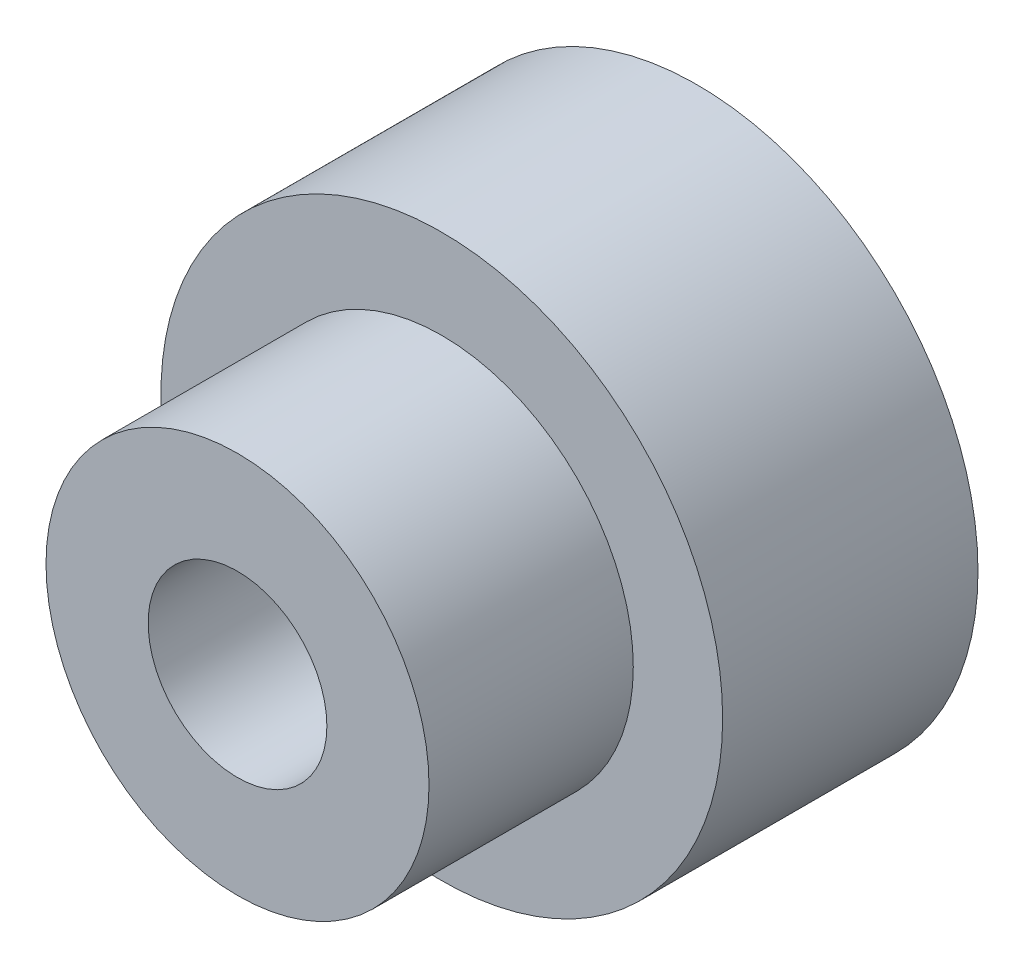
SolidWorks part; units mm, degrees
ref_plane "前视基准面" through (0, 0, 0) normal (0, 0, 1) x (1, 0, 0)
ref_plane "上视基准面" through (0, 0, 0) normal (0, 1, 0) x (1, 0, 0)
ref_plane "右视基准面" through (0, 0, 0) normal (1, 0, 0) x (0, 0, -1)
sketch "草图1" plane through (0, 0, 0) normal (0, 0, 1) x (1, 0, 0)
  circle A0 centre (0, 0) radius 11
  dimension "D1" = 22
extrude "凸台-拉伸1" add sketch "草图1" along normal blind 10
sketch "草图2" plane through (0, 0, 10) normal (0, 0, 1) x (1, 0, 0)
  circle A0 centre (0, 0) radius 7.5
  dimension "D1" = 15
extrude "凸台-拉伸2" add sketch "草图2" along normal blind 8
sketch "草图3" plane through (0, 0, 18) normal (0, 0, 1) x (1, 0, 0)
  circle A0 centre (0, 0) radius 3.5
  dimension "D1" = 7
extrude "切除-拉伸1" cut sketch "草图3" against normal through all
